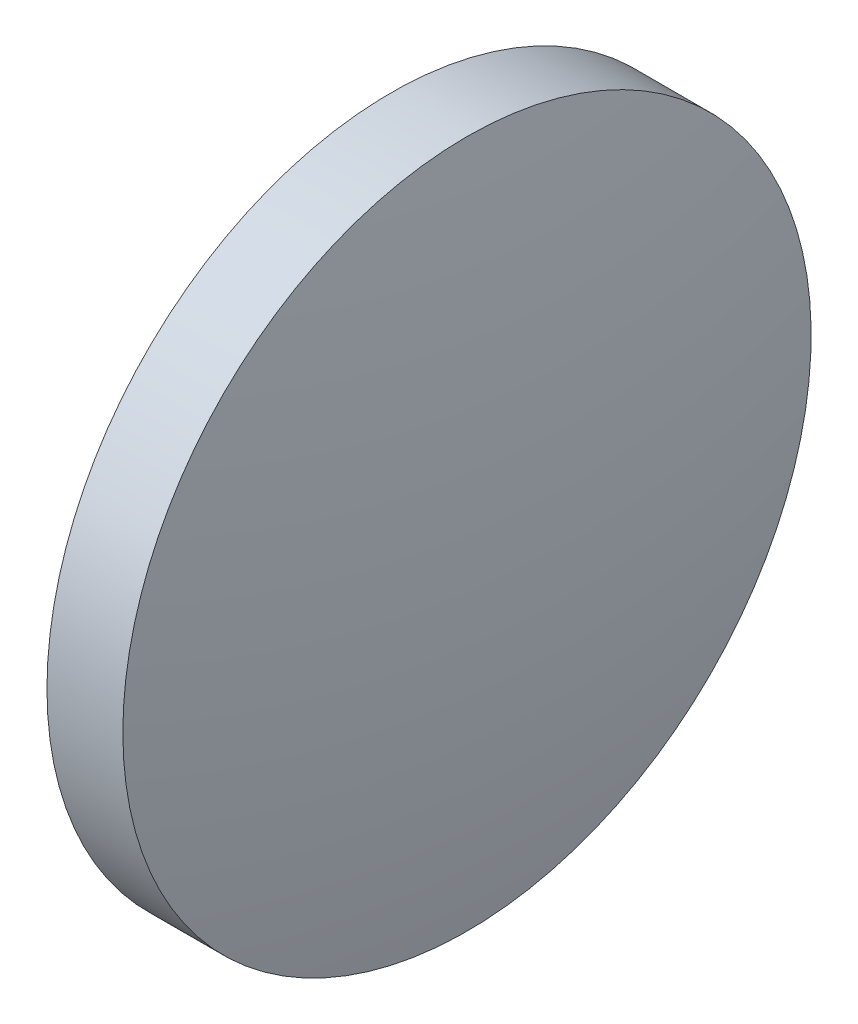
SolidWorks part; units mm, degrees
ref_plane "前视基准面" through (0, 0, 0) normal (0, 0, 1) x (1, 0, 0)
ref_plane "上视基准面" through (0, 0, 0) normal (0, 1, 0) x (1, 0, 0)
ref_plane "右视基准面" through (0, 0, 0) normal (1, 0, 0) x (0, 0, -1)
sketch "草图1" plane through (0, 0, 0) normal (0, 0, 1) x (1, 0, 0)
  line L0 (192.6678, 18.7324) -> (202.0657, 18.7324) construction
  line L1 (195.5369, 18.7324) -> (195.5369, 25.0824)
  line L2 (197.5369, 18.7324) -> (195.5369, 18.7324)
  line L5 (195.5369, 25.0824) -> (196.9369, 25.0824)
  arc A0 (197.5369, 18.7324) -> (196.9369, 25.0824) centre (163.6348, 18.7324) ccw
revolve "旋转1" add sketch "草图1" angle 360 about L0
